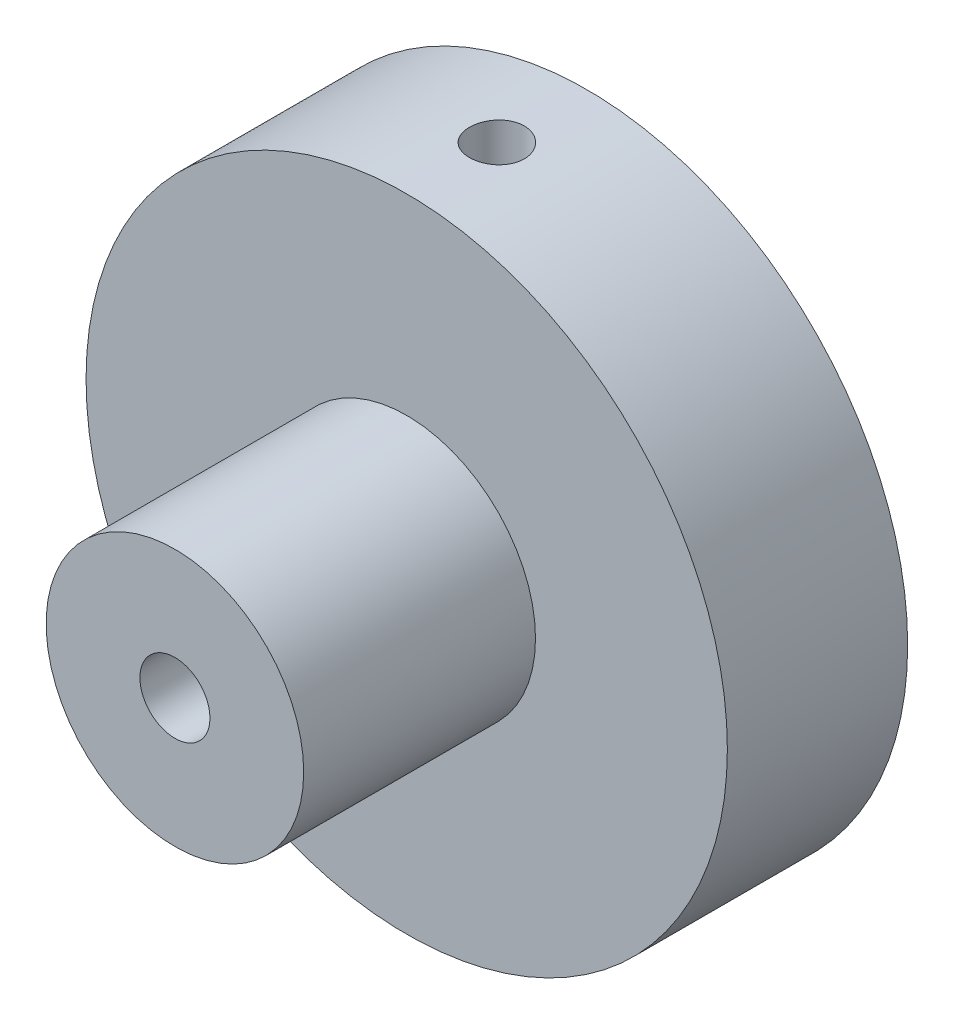
SolidWorks part; units mm, degrees
ref_plane "Front Plane" through (0, 0, 0) normal (0, 0, 1) x (1, 0, 0)
ref_plane "Top Plane" through (0, 0, 0) normal (0, 1, 0) x (1, 0, 0)
ref_plane "Right Plane" through (0, 0, 0) normal (1, 0, 0) x (0, 0, -1)
sketch "Sketch1" plane through (0, 0, 0) normal (0, 0, 1) x (1, 0, 0)
  circle A0 centre (0, 0) radius 15.8115
  dimension "D1" = 31.623
extrude "Boss-Extrude1" add sketch "Sketch1" along normal blind 25.4
sketch "Sketch2" plane through (0, 0, 25.4) normal (0, 0, 1) x (1, 0, 0)
  circle A0 centre (0, 0) radius 6.35
  dimension "D1" = 12.7
extrude "Cut-Extrude1" cut sketch "Sketch2" against normal blind 16.51 flip side to cut
hole_wizard "#8-32 Tapped Hole1" positions "Sketch4" profile "Sketch3" tap size "#8-32" standard "ANSI Inch" end condition through all
sketch "Sketch4" plane through (0, 0, 25.4) normal (0, 0, 1) x (1, 0, 0)
  point P0 (0, 0)
sketch "Sketch3" plane through (0, 0, 25.4) normal (1, 0, 0) x (0, -1, 0)
  line L0 (0, 0) -> (0, 25.4)
  line L1 (0, 25.4) -> (1.7272, 25.4)
  line L2 (1.7272, 25.4) -> (1.7272, 0)
  line L5 (1.7272, 0) -> (0, 0)
  line L11 (0, -6.35) -> (0, 107.95) construction
  dimension "Thread Major Dia." = 3.4544
  dimension "Thru Tap Drill Depth" = 25.4
sketch "Sketch5" plane through (0, 0, 0) normal (0, 0, -1) x (-1, 0, 0)
  circle A0 centre (0, 0) radius 1.5875
  dimension "D1" = 3.175
extrude "Cut-Extrude2" [suppressed] cut sketch "Sketch5" against normal through all
hole_wizard "#6-32 Tapped Hole2" positions "Sketch7" profile "Sketch6" tap size "#6-32" standard "ANSI Inch"
sketch "Sketch7" plane through (0, 0, 0) normal (0, 0, -1) x (-1, 0, 0)
  point P0 (-6.35, 0)
  point P2 (6.35, 0)
  dimension "D1" = 6.35
  dimension "D2" = 6.35
sketch "Sketch6" plane through (6.35, 0, 0) normal (1, 0, 0) x (0, 1, 0)
  line L0 (0, 0) -> (0, 7.6707)
  line L1 (0, 7.6707) -> (1.3525, 6.858)
  line L2 (1.3525, 6.858) -> (1.3525, 0)
  line L5 (1.3525, 0) -> (0, 0)
  line L10 (0, 7.6707) -> (-1.3526, 6.858) construction
  line L11 (0, -6.35) -> (0, 107.95) construction
  dimension "Tap Drill Dia." = 2.7051
  dimension "Tap Drill Depth" = 6.858
  dimension "Drill Angle" = 118
hole_wizard "#6-32 Tapped Hole3" positions "3DSketch1" profile "Sketch8" tap size "#6-32" standard "ANSI Inch"
sketch3d "3DSketch1"
  point P0 (0, 15.8115, 4.445)
sketch "Sketch8" plane through (0, 15.8115, 4.445) normal (1, 0, 0) x (0, 0, 1)
  line L0 (0, 0) -> (0, 6.9087)
  line L1 (0, 6.9087) -> (1.3525, 6.096)
  line L2 (1.3525, 6.096) -> (1.3525, 0)
  line L5 (1.3525, 0) -> (0, 0)
  line L10 (0, 6.9087) -> (-1.3526, 6.096) construction
  line L11 (0, -6.35) -> (0, 107.95) construction
  dimension "Tap Drill Dia." = 2.7051
  dimension "Tap Drill Depth" = 6.096
  dimension "Drill Angle" = 118
sketch "Sketch9" plane through (0, 0, 25.4) normal (0, 0, 1) x (1, 0, 0)
  circle A0 centre (0, 0) radius 6.35
extrude "Cut-Extrude3" cut sketch "Sketch9" against normal blind 5.08
